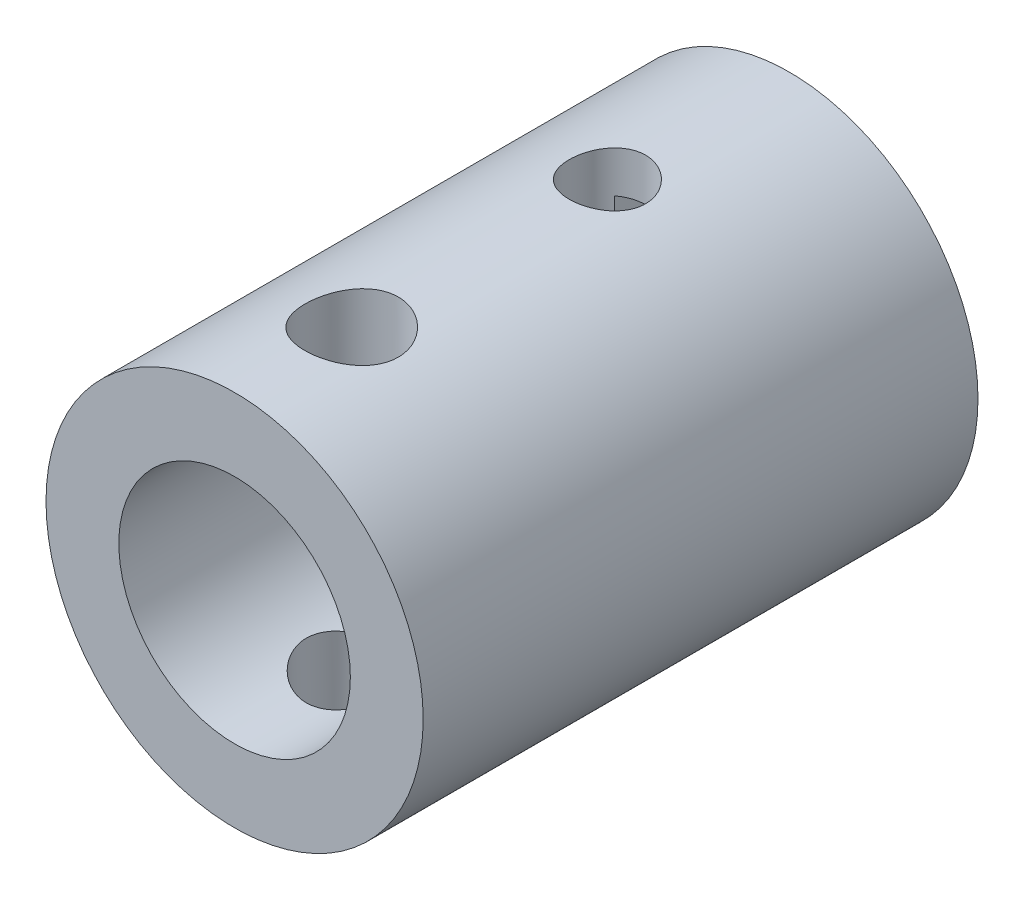
SolidWorks part; units mm, degrees
ref_plane "Front Plane" through (0, 0, 0) normal (0, 0, 1) x (1, 0, 0)
ref_plane "Top Plane" through (0, 0, 0) normal (0, 1, 0) x (1, 0, 0)
ref_plane "Right Plane" through (0, 0, 0) normal (1, 0, 0) x (0, 0, -1)
sketch "Sketch1" plane through (0, 0, 0) normal (0, 0, 1) x (1, 0, 0)
  circle A0 centre (0, 0) radius 25.9
extrude "Boss-Extrude1" add sketch "Sketch1" along normal blind 76.2
sketch "Sketch2" plane through (0, 0, 76.2) normal (0, 0, 1) x (1, 0, 0)
  circle A0 centre (0, 0) radius 15.9
extrude "Cut-Extrude1" cut sketch "Sketch2" against normal through all
hole_wizard "Ø10.5 (10.5) Diameter Hole1" positions "3DSketch1" profile "Sketch3" hole size "Ø10.5" standard "Ansi Metric"
sketch3d "3DSketch1"
  line L4 (0, 0, 0) -> (0, 25.9, 0)
  line L5 (0, 25.9, 0) -> (0, 25.9, 25)
  circle A0 centre (0, 0, 0) radius 25.9 construction
  point P0 (0, 25.9, 25)
  point P7 (0, 0, 25.9)
  dimension "D2" = 25
sketch "Sketch3" plane through (0, 25.9, 25) normal (1, 0, 0) x (0, 0, 1)
  line L0 (0, 0) -> (0, 23.1545)
  line L1 (0, 23.1545) -> (5.25, 20)
  line L2 (5.25, 20) -> (5.25, 0)
  line L5 (5.25, 0) -> (0, 0)
  line L10 (0, 23.1545) -> (-5.25, 20) construction
  line L11 (0, -6.35) -> (0, 107.95) construction
  dimension "Hole Dia." = 10.5
  dimension "Hole Depth" = 20
  dimension "Drill Angle" = 118
hole_wizard "Ø12.8 (12.8) Diameter Hole1" positions "3DSketch2" profile "Sketch4" hole size "Ø12.8" standard "Ansi Metric"
sketch3d "3DSketch2"
  line L0 (-3.6112, 25.647, 28.8107) -> (-3.6112, 25.647, 0)
  line L4 (0, 0, 0) -> (-0.1194, 25.8997, 0)
  line L5 (-0.1194, 25.8997, 0) -> (-0.1194, 25.8997, 60)
  circle A0 centre (0, 0, 0) radius 25.9 construction
  spline S0 degree 3 poles (0.3478, 25.9, 30.25) (-0.3478, 25.9, 30.25) (-0.6896, 25.893, 30.2158) (-1.1938, 25.873, 30.1153) (-1.3604, 25.8648, 30.0736) (-1.6907, 25.8453, 29.9733) (-1.8546, 25.834, 29.9145) (-2.3311, 25.7969, 29.7167) (-2.6323, 25.7675, 29.5553) (-3.2023, 25.7029, 29.1744) (-3.4715, 25.6675, 28.9532) (-3.9543, 25.5975, 28.4703) (-4.1713, 25.5626, 28.2066) (-4.5551, 25.497, 27.633) (-4.7176, 25.4671, 27.3289) (-4.9142, 25.4296, 26.8554) (-4.9721, 25.4183, 26.6943) (-5.0723, 25.3985, 26.3652) (-5.1148, 25.39, 26.1963) (-5.2162, 25.3694, 25.6877) (-5.2498, 25.3624, 25.3465) (-5.2502, 25.3623, 24.6598) (-5.2159, 25.3695, 24.3109) (-5.0816, 25.3967, 23.6369) (-4.9822, 25.4166, 23.3092) (-4.7844, 25.4544, 22.8316) (-4.7099, 25.4683, 22.6743) (-4.5477, 25.4978, 22.3712) (-4.4596, 25.5134, 22.2245) (-4.175, 25.562, 21.7987) (-3.957, 25.5971, 21.5325) (-3.4692, 25.6678, 21.0445) (-3.2052, 25.7025, 20.8279) (-2.6375, 25.7669, 20.4478) (-2.3301, 25.7969, 20.2829) (-1.6957, 25.8464, 20.0195) (-1.3684, 25.866, 19.9198) (-0.6937, 25.8929, 19.7847) (-0.3452, 25.9, 19.7501) (0.341, 25.9, 19.7499) (0.6826, 25.8932, 19.783) (1.3629, 25.8664, 19.9181) (1.6928, 25.8466, 20.0186) (2.1669, 25.8097, 20.215) (2.3218, 25.7962, 20.2882) (2.6254, 25.767, 20.4503) (2.7745, 25.7514, 20.5397) (3.2032, 25.7028, 20.8262) (3.4669, 25.6681, 21.0427) (3.9513, 25.598, 21.5263) (4.1727, 25.5624, 21.7956) (4.553, 25.4974, 22.3637) (4.7147, 25.4676, 22.6647) (4.9134, 25.4298, 23.1425) (4.9723, 25.4183, 23.3063) (5.0725, 25.3985, 23.6354) (5.1143, 25.3901, 23.8017) (5.2151, 25.3696, 24.3053) (5.2498, 25.3624, 24.6497) (5.2502, 25.3623, 25.343) (5.2165, 25.3693, 25.6845) (5.0831, 25.3964, 26.3575) (4.9816, 25.4168, 26.6923) (4.7188, 25.4668, 27.3265) (4.5579, 25.4965, 27.628) (4.2718, 25.5455, 28.0568) (4.1684, 25.5626, 28.1964) (3.9504, 25.5972, 28.4621) (3.8356, 25.6147, 28.5888) (3.474, 25.6671, 28.951) (3.2098, 25.702, 29.1689) (2.635, 25.7672, 29.554) (2.3332, 25.7966, 29.7155) (1.7018, 25.846, 29.9783) (1.3687, 25.866, 30.0802) (0.6911, 25.893, 30.2158) (0.3478, 25.9, 30.25) (-0.3478, 25.9, 30.25) (-0.6896, 25.893, 30.2158) knots -0.03125 -0.03125 0 0 0.03125 0.03125 0.046875 0.046875 0.0625 0.0625 0.09375 0.09375 0.125 0.125 0.15625 0.15625 0.1875 0.1875 0.203125 0.203125 0.21875 0.21875 0.25 0.25 0.28125 0.28125 0.3125 0.3125 0.328125 0.328125 0.34375 0.34375 0.375 0.375 0.40625 0.40625 0.4375 0.4375 0.46875 0.46875 0.5 0.5 0.53125 0.53125 0.5625 0.5625 0.578125 0.578125 0.59375 0.59375 0.625 0.625 0.65625 0.65625 0.6875 0.6875 0.703125 0.703125 0.71875 0.71875 0.75 0.75 0.78125 0.78125 0.8125 0.8125 0.84375 0.84375 0.859375 0.859375 0.875 0.875 0.90625 0.90625 0.9375 0.9375 0.96875 0.96875 1 1 1.03125 1.03125 1.046875 only from (0, 25.9, 30.25) to (0, 25.9, 30.25) construction
  point P0 (-0.1194, 25.8997, 60)
  point P6 (0, 0, 25.9)
  dimension "D2" = 60
sketch "Sketch4" plane through (-0.1194, 25.8997, 60) normal (0, 0, 1) x (-1, -0.0046, 0)
  line L0 (0, 0) -> (0, 303.8455)
  line L1 (0, 303.8455) -> (6.4, 300)
  line L2 (6.4, 300) -> (6.4, 0)
  line L5 (6.4, 0) -> (0, 0)
  line L10 (0, 303.8455) -> (-6.4, 300) construction
  line L11 (0, -6.35) -> (0, 107.95) construction
  dimension "Hole Dia." = 12.8
  dimension "Hole Depth" = 300
  dimension "Drill Angle" = 118
sketch "Sketch5" plane through (0, 0, 0) normal (0, 0, -1) x (-1, 0, 0)
  line L1 (3.175, -20) -> (-3.175, -20)
  line L2 (3.175, -20) -> (3.175, 20)
  line L3 (3.175, 20) -> (-3.175, 20)
  line L4 (-3.175, -20) -> (-3.175, 20)
  line L5 (3.175, -20) -> (-3.175, 20) construction
  line L6 (3.175, 20) -> (-3.175, -20) construction
  line L7 (-3.175, 20) -> (3.175, 20)
  line L8 (-3.175, 20) -> (-3.175, 12.4094)
  line L9 (-3.175, 12.4094) -> (3.175, 12.4094)
  line L10 (3.175, 20) -> (3.175, 12.4094)
  point P0 (0, 0)
  circle M1 centre (0, 0) radius 15.9
  dimension "D1" = 6.35
  dimension "D2" = 40
extrude "Cut-Extrude2" cut sketch "Sketch5" against normal blind 35 contours L4 L2 L3 M1
